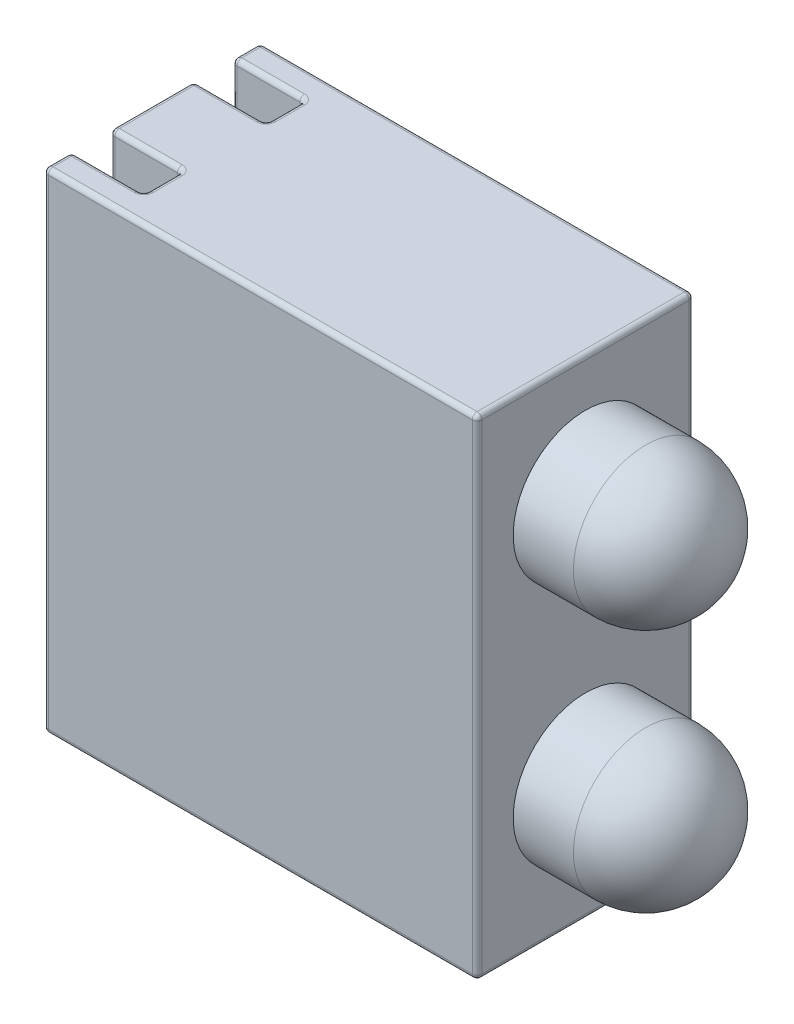
SolidWorks part; units mm, degrees
material "ABS"
ref_plane "Front Plane" through (0, 0, 0) normal (0, 0, 1) x (1, 0, 0)
ref_plane "Top Plane" through (0, 0, 0) normal (0, 1, 0) x (1, 0, 0)
ref_plane "Right Plane" through (0, 0, 0) normal (1, 0, 0) x (0, 0, -1)
sketch "Sketch1" plane through (0, 0, 0) normal (0, 0, 1) x (1, 0, 0)
  line L1 (9, 10.16) -> (0, 10.16)
  line L2 (9, 10.16) -> (9, 0)
  line L3 (9, 0) -> (0, 0)
  line L4 (0, 10.16) -> (0, 0)
  line L5 (9, 10.16) -> (0, 0) construction
  line L6 (9, 0) -> (0, 10.16) construction
  point P0 (4.5, 5.08)
  dimension "D1" = 10.16
  dimension "D2" = 9
extrude "Boss-Extrude1" add sketch "Sketch1" along normal mid plane 4.5
sketch "Sketch2" plane through (0, 0, 0) normal (-1, 0, 0) x (0, 0, 1)
  line L0 (2.25, 10.16) -> (-2.25, 10.16) construction
  line L1 (-1.67, 10.16) -> (-0.87, 10.16)
  line L2 (-1.67, 10.16) -> (-1.67, 0)
  line L3 (-1.67, 0) -> (-0.87, 0)
  line L4 (-0.87, 10.16) -> (-0.87, 0)
  line L5 (-1.67, 10.16) -> (-0.87, 0) construction
  line L6 (-1.67, 0) -> (-0.87, 10.16) construction
  line L7 (2.25, 0) -> (-2.25, 0) construction
  line L8 (0, 0) -> (0, 2.2789) construction
  line L9 (1.67, 10.16) -> (0.87, 10.16)
  line L10 (1.67, 10.16) -> (1.67, 0)
  line L11 (0.87, 10.16) -> (0.87, 0)
  line L12 (1.67, 0) -> (0.87, 0)
  point P0 (-1.27, 5.08)
  dimension "D1" = 0.8
  dimension "D2" = 1.27
extrude "Cut-Extrude1" cut sketch "Sketch2" against normal blind 1.5
sketch "Sketch3" plane through (0, 0, 0) normal (0, 0, 1) x (1, 0, 0)
  line L0 (10.25, 9.16) -> (9, 9.16)
  line L1 (9, 0) -> (9, 10.16) construction
  line L3 (9, 9.16) -> (9, 7.66)
  line L4 (9, 10.16) -> (0, 10.16) construction
  line L5 (11.75, 7.66) -> (9, 7.66)
  arc A0 (11.75, 7.66) -> (10.25, 9.16) centre (10.25, 7.66) ccw
  dimension "D1" = 1.5
  dimension "D2" = 1.25
  dimension "D3" = 1
revolve "Revolve4" add sketch "Sketch3" angle 360 about L5
pattern_linear "LPattern1" count 2 spacing 5.08 along (0, -1, 0) of "Revolve4"
fillet "Fillet1" radius 0.1 36 edges at (1.5, 5.08, -1.67) (0, 5.08, -1.67) (1.5, 5.08, -0.87) (0, 5.08, -0.87) (1.5, 5.08, 0.87) (0, 5.08, 0.87) (1.5, 5.08, 1.67) (0, 5.08, 1.67) (0.75, 0, 0.87) (1.5, 0, 1.27) (0.75, 0, 1.67) (0, 0, 1.96) (9, 0, 0) (0, 0, -1.96) (0.75, 0, -1.67) (1.5, 0, -1.27) (0.75, 0, -0.87) (0, 0, 0) (0.75, 10.16, -1.67) (0, 10.16, -1.96) (9, 10.16, 0) (0, 10.16, 1.96) (0.75, 10.16, 1.67) (1.5, 10.16, 1.27) (0.75, 10.16, 0.87) (0, 10.16, 0) (0.75, 10.16, -0.87) (1.5, 10.16, -1.27) (4.5, 0, -2.25) (9, 5.08, -2.25) (4.5, 10.16, -2.25) (0, 5.08, -2.25) (4.5, 10.16, 2.25) (9, 5.08, 2.25) (4.5, 0, 2.25) (0, 5.08, 2.25)
